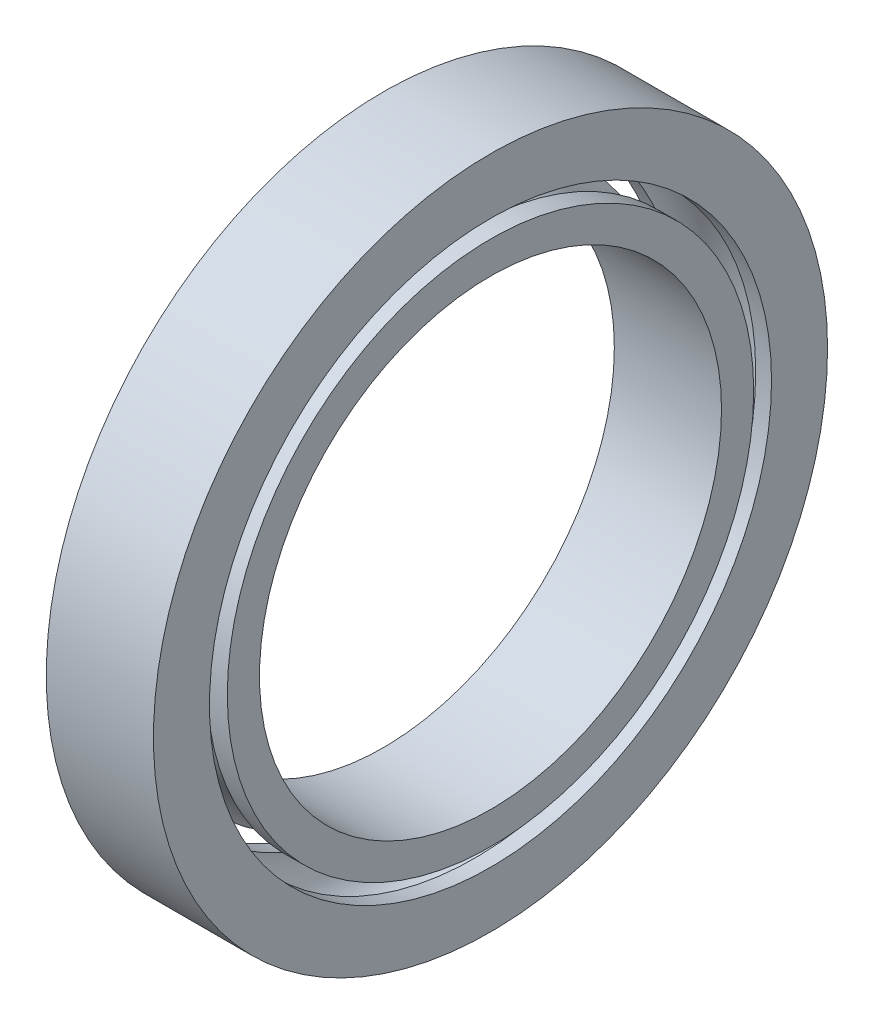
SolidWorks part; units mm, degrees
ref_plane "Front Plane" through (0, 0, 0) normal (0, 0, 1) x (1, 0, 0)
ref_plane "Top Plane" through (0, 0, 0) normal (0, 1, 0) x (1, 0, 0)
ref_plane "Right Plane" through (0, 0, 0) normal (1, 0, 0) x (0, 0, -1)
sketch "Sketch1" plane through (0, 0, 0) normal (0, 0, 1) x (1, 0, 0)
  line L0 (-16.1278, 120) -> (-22.8849, 120)
  line L1 (22.8849, 120) -> (16.1278, 120)
  line L2 (22.8849, 120) -> (22.8849, 143.9211)
  line L3 (22.8849, 143.9211) -> (-22.8849, 143.9211)
  line L4 (-22.8849, 120) -> (-22.8849, 143.9211)
  line L5 (22.8849, 98.6434) -> (-22.8849, 98.6434)
  line L6 (22.8849, 98.6434) -> (22.8849, 112.3852)
  line L7 (22.8849, 112.3852) -> (14.217, 112.3852)
  line L8 (-22.8849, 98.6434) -> (-22.8849, 112.3852)
  line L9 (-14.217, 112.3852) -> (-22.8849, 112.3852)
  line L11 (89.1035, 0) -> (-107.0918, 0) construction
  arc A0 (-14.217, 112.3852) -> (14.217, 112.3852) centre (0, 120) ccw
  arc A1 (16.1278, 120) -> (-16.1278, 120) centre (0, 120) ccw
  point P7 (5.8031, -132.9098)
  dimension "D1" = 120
  dimension "D2" = 16.1278
revolve "Revolve5" add sketch "Sketch1" angle 360 about L11
